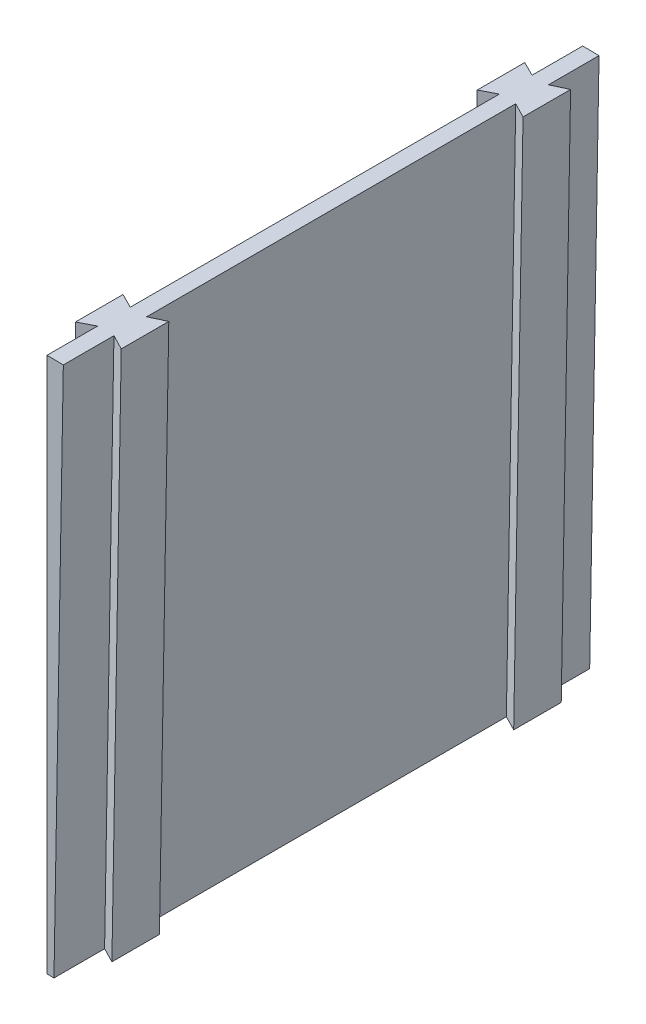
SolidWorks part; units mm, degrees
ref_plane "Front Plane" through (0, 0, 0) normal (0, 0, 1) x (1, 0, 0)
ref_plane "Top Plane" through (0, 0, 0) normal (0, 1, 0) x (1, 0, 0)
ref_plane "Right Plane" through (0, 0, 0) normal (1, 0, 0) x (0, 0, -1)
sketch "Sketch1" plane through (0, 0, 0) normal (0, 0, 1) x (1, 0, 0)
  line L0 (0, 76.2) -> (0, 177.8)
  line L1 (1.3299, 76.1884) -> (3.103, 177.7729)
  circle A0 centre (0, 0) radius 76.2 construction
  circle A1 centre (0, 0) radius 177.8 construction
  arc A2 (0, 177.8) -> (3.103, 177.7729) centre (0, 0) cw
  arc A3 (0, 76.2) -> (1.3299, 76.1884) centre (0, 0) cw
  dimension "D1" = 152.4
  dimension "D2" = 101.6
  dimension "D3" = 1
extrude "Boss-Extrude1" add sketch "Sketch1" along normal blind 101.6
ref_plane "Plane1" through (1.3299, 76.1884, 0) normal (-0.0175, -0.9998, 0) x (0, 0, -1)
sketch "Sketch2" plane through (1.3299, 76.1884, 0) normal (-0.0175, -0.9998, 0) x (0, 0, -1)
  line L10 (-92.0002, 0) -> (-93.4085, 2.794)
  line L15 (-101.6, 0) -> (0, 0) construction
  line L19 (-93.4085, 2.794) -> (-84.3915, 2.794)
  line L36 (-84.3915, 2.794) -> (-85.7998, 0)
  line L37 (-15.8002, 0) -> (-9.5998, 0)
  line L45 (-50.8, -1.3299) -> (-50.8, 25.7132) construction
  line L46 (-101.6, -1.3299) -> (0, -1.3299) construction
  line L55 (-85.7998, 0) -> (-92.0002, 0)
  line L56 (-17.2085, 2.794) -> (-15.8002, 0)
  line L57 (-8.1915, 2.794) -> (-17.2085, 2.794)
  line L58 (-9.5998, 0) -> (-8.1915, 2.794)
  point P4 (-88.9, 0)
  dimension "D1" = 63.25
  dimension "D2" = 9.017
  dimension "D3" = 2.794
  dimension "D4" = 12.7
extrude "Boss-Extrude2" add sketch "Sketch2" against normal up to surface (101.6 mm away)
ref_plane "Plane2" through (0, 76.2, 0) normal (0, -1, 0) x (0, 0, -1)
sketch "Sketch3" plane through (0, 76.2, 0) normal (0, -1, 0) x (0, 0, -1)
  line L0 (-92.0002, 0) -> (-93.4085, -2.7936)
  line L2 (-101.6, 0) -> (0, 0) construction
  line L13 (-93.4085, -2.7936) -> (-84.3915, -2.7936)
  line L14 (-84.3915, -2.7936) -> (-85.7998, 0)
  line L22 (-50.8, 0) -> (-50.8, 15.717) construction
  line L55 (-85.7998, 0) -> (-92.0002, 0)
  line L56 (-92.0002, 1.3299) -> (-85.7998, 1.3299) construction
  line L57 (-84.3915, 4.1234) -> (-93.4085, 4.1234) construction
  line L58 (-93.4085, 4.1234) -> (-92.0002, 1.3299) construction
  line L59 (-15.8002, 0) -> (-9.5998, 0)
  line L60 (-17.2085, -2.7936) -> (-15.8002, 0)
  line L61 (-8.1915, -2.7936) -> (-17.2085, -2.7936)
  line L62 (-9.5998, 0) -> (-8.1915, -2.7936)
  point P12 (-88.9, 1.3299)
  point P13 (-88.9, 0)
extrude "Boss-Extrude3" add sketch "Sketch3" against normal up to surface (101.5781 mm away)
